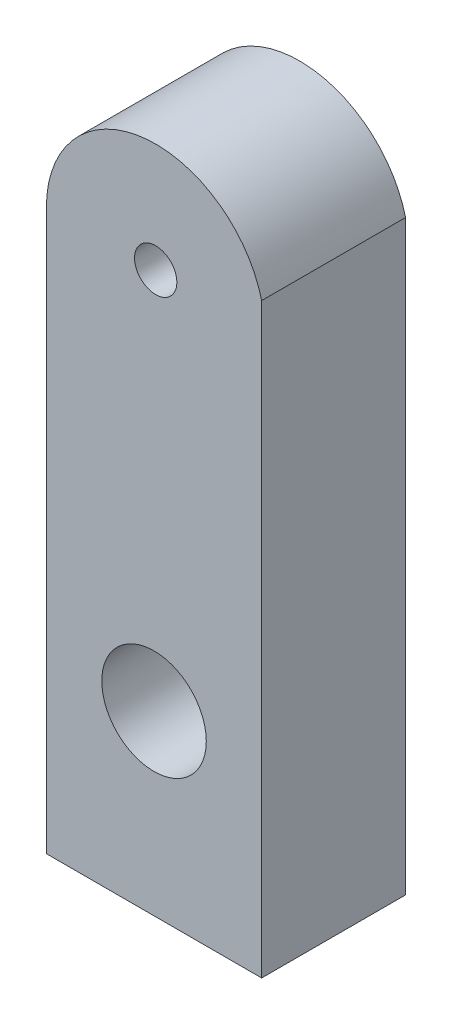
SolidWorks part; units mm, degrees
ref_plane "Front" through (0, 0, 0) normal (0, 0, 1) x (1, 0, 0)
ref_plane "Top" through (0, 0, 0) normal (0, 1, 0) x (1, 0, 0)
ref_plane "Right" through (0, 0, 0) normal (1, 0, 0) x (0, 0, -1)
sketch "Sketch1" plane through (0, 0, 0) normal (0, 0, 1) x (1, 0, 0)
  line L0 (-0.1946, -45.214) -> (-0.1946, -66.1519) construction
  line L2 (-12.907, 0) -> (-12.907, -66.1519)
  line L3 (-12.907, -66.1519) -> (12.5178, -66.1519)
  line L4 (12.5178, 3.1456) -> (12.5178, -66.1519)
  arc A0 (12.5178, 3.1456) -> (-12.907, 0) centre (0, 0) ccw
  circle A1 centre (0, 0) radius 2.5
  circle A2 centre (0, 0) radius 2.5 construction
  circle A3 centre (-0.1946, -45.214) radius 6.1718
  arc A4 (6.8925, -50.9219) -> (49.887, -12.3221) centre (0, 0) ccw construction
  arc A5 (5.2368, -38.6899) -> (37.9036, -9.3622) centre (0, 0) ccw construction
extrude "Boss-Extrude1" add sketch "Sketch1" along normal up to surface (17 mm away)
